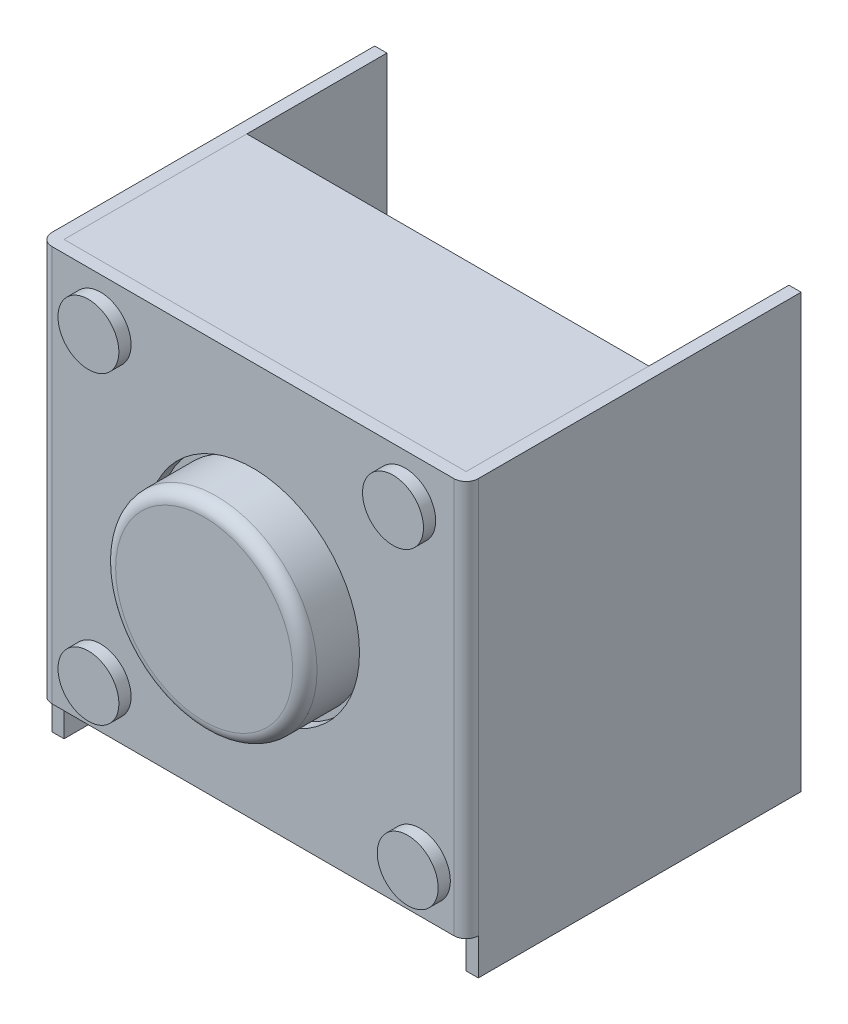
SolidWorks part; units mm, degrees
material "Duranickel(R) 301"
ref_plane "Alzado" through (0, 0, 0) normal (0, 0, 1) x (1, 0, 0)
ref_plane "Planta" through (0, 0, 0) normal (0, 1, 0) x (1, 0, 0)
ref_plane "Vista lateral" through (0, 0, 0) normal (1, 0, 0) x (0, 0, -1)
sketch "Croquis1" plane through (0, 0, 0) normal (0, 0, 1) x (1, 0, 0)
  line L1 (-3.5, 3.25) -> (3.5, 3.25)
  line L2 (-3.5, 3.25) -> (-3.5, -3.25)
  line L3 (-3.5, -3.25) -> (3.5, -3.25)
  line L4 (3.5, 3.25) -> (3.5, -3.25)
  circle A0 centre (0, 0) radius 1.75
  circle A1 centre (2.5, 2.5) radius 0.5
  circle A2 centre (2.7414, -2.5) radius 0.5
  circle A3 centre (-2.5, -2.5) radius 0.5
  circle A4 centre (-2.5, 2.5) radius 0.5
  dimension "D5" = 3.5
  dimension "D6" = 1
  dimension "D7" = 1
  dimension "D8" = 1
  dimension "D9" = 1
  dimension "D1" = 7
  dimension "D2" = 6.5
  dimension "D3" = 3.5
  dimension "D4" = 3.25
  dimension "D10" = 5
  dimension "D11" = 5
  dimension "D12" = 2.5
  dimension "D13" = 2.5
  dimension "D14" = 5
extrude "Extruir1" add sketch "Croquis1" along normal blind 0.2
sketch "Croquis2" plane through (3.5, 0, 0) normal (1, 0, 0) x (0, 0, -1)
  line L0 (-0.2, 3.25) -> (5.3, 3.25)
  line L1 (5.3, 3.25) -> (5.3, -3.85)
  line L2 (5.3, -3.85) -> (0, -3.85)
  line L3 (0, -3.85) -> (0, -3.25)
  line L4 (0, -3.25) -> (-0.2, -3.25)
  line L5 (-0.2, -3.25) -> (-0.2, 3.25)
  dimension "D1" = 7.1
  dimension "D2" = 5.5
extrude "Extruir2" add sketch "Croquis2" against normal blind 0.2
mirror "Simetría1" about plane through (0, 0, 0) normal (1, 0, 0) of "Extruir2"
fillet "Redondeo1" radius 0.2 2 edges at (-3.5, 0, 0.2) (3.5, 0, 0.2)
sketch "Croquis3" plane through (0, 0, 0) normal (0, 0, -1) x (-1, 0, 0)
  line L1 (-3.3, 3.25) -> (3.3, 3.25)
  line L2 (-3.3, 3.25) -> (-3.3, -3.25)
  line L3 (-3.3, -3.25) -> (3.3, -3.25)
  line L4 (3.3, 3.25) -> (3.3, -3.25)
extrude "Extruir3" add sketch "Croquis3" along normal blind 3 separate body
sketch "Croquis4" plane through (0, 0, 0) normal (0, 0, 1) x (1, 0, 0)
  circle A0 centre (0, 0) radius 1.6528
extrude "Extruir5" add sketch "Croquis4" along normal blind 1 separate body
sketch "Croquis5" plane through (0, 0, 0) normal (0, 0, 1) x (1, 0, 0)
  circle A0 centre (2.5, 2.5) radius 0.5
  circle A1 centre (-2.5, 2.5) radius 0.5
  circle A2 centre (-2.5, -2.5) radius 0.5
  circle A3 centre (2.7414, -2.5) radius 0.5
  dimension "D1" = 1
  dimension "D2" = 1
  dimension "D3" = 1
  dimension "D4" = 1
extrude "Extruir6" add sketch "Croquis5" along normal blind 0.4 separate body
fillet "Redondeo2" radius 0.2 1 edges at (1.6528, 0, 1)
